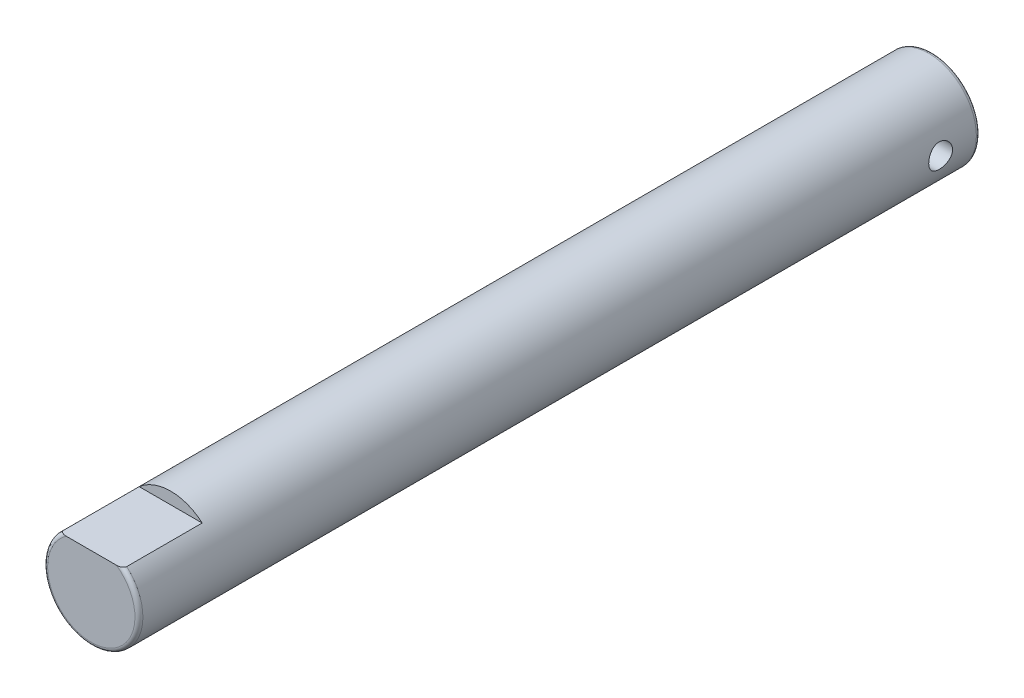
SolidWorks part; units mm, degrees
material "Stainless Steel (ferritic)"
ref_plane "Front Plane" through (0, 0, 0) normal (0, 0, 1) x (1, 0, 0)
ref_plane "Top Plane" through (0, 0, 0) normal (0, 1, 0) x (1, 0, 0)
ref_plane "Right Plane" through (0, 0, 0) normal (1, 0, 0) x (0, 0, -1)
sketch "Sketch1" plane through (0, 0, 0) normal (0, 0, 1) x (1, 0, 0)
  circle A0 centre (0, 0) radius 3
  dimension "D1" = 6
extrude "Boss-Extrude1" add sketch "Sketch1" along normal blind 53
fillet "Fillet1" radius 0.25 2 edges at (3, 0, 0) (3, 0, 53)
sketch "Sketch2" plane through (0, 0, 0) normal (1, 0, 0) x (0, 0, -1)
  line L0 (-0.25, 3) -> (-52.75, 3) construction
  circle A0 centre (-2.5, 0) radius 0.75
  dimension "D1" = 1.5
  dimension "D2" = 3
  dimension "D3" = 2.5
extrude "Cut-Extrude1" cut sketch "Sketch2" against normal through all both and the other way through all
ref_plane "Plane1" through (0, 2.25, 0) normal (0, 1, 0) x (1, 0, 0)
sketch "Sketch4" plane through (0, 2.25, 0) normal (0, 1, 0) x (1, 0, 0)
  line L0 (2.75, 0) -> (-2.75, 0) construction
  line L1 (-6.7012, -48) -> (8.2988, -48)
  line L2 (-6.7012, -48) -> (-6.7012, -53)
  line L3 (-6.7012, -53) -> (8.2988, -53)
  line L4 (8.2988, -48) -> (8.2988, -53)
  dimension "D1" = 53
  dimension "D2" = 5
  dimension "D3" = 15
  dimension "D4" = 8.2988
extrude "Cut-Extrude2" cut sketch "Sketch4" along normal through all both 53
